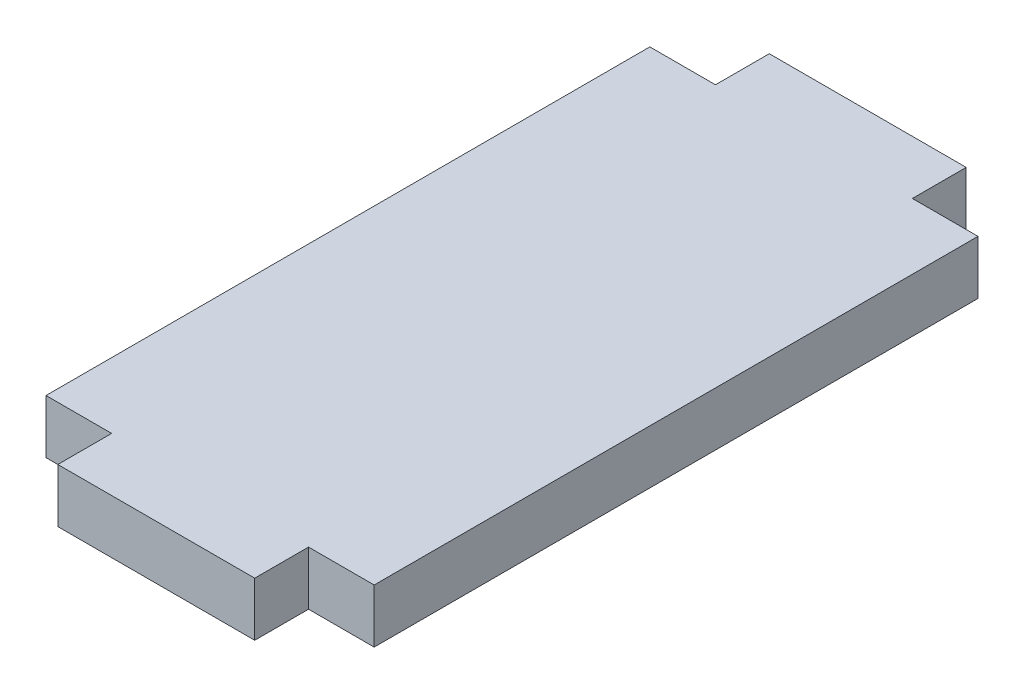
SolidWorks part; units mm, degrees
material "Corrugated Paper"
ref_plane "Front" through (0, 0, 0) normal (0, 0, 1) x (1, 0, 0)
ref_plane "Top" through (0, 0, 0) normal (0, 1, 0) x (1, 0, 0)
ref_plane "Right" through (0, 0, 0) normal (1, 0, 0) x (0, 0, -1)
sketch "Sketch1" plane through (0, 0, 0) normal (0, 1, 0) x (1, 0, 0)
  line L0 (-12.5, 0) -> (12.5, 0) construction
  line L1 (-12.5, -23) -> (12.5, -23) construction
  line L2 (-12.5, -23) -> (-12.5, 23)
  line L3 (-12.5, 23) -> (12.5, 23) construction
  line L4 (12.5, -23) -> (12.5, 23)
  line L5 (-12.5, -23) -> (12.5, 23) construction
  line L6 (-12.5, 23) -> (12.5, -23) construction
  line L7 (-12.5, 23) -> (-7.5, 23)
  line L8 (7.5, -23) -> (7.5, -27.1)
  line L9 (-7.5, 23) -> (-7.5, 27.1)
  line L10 (-7.5, 27.1) -> (7.5, 27.1)
  line L11 (7.5, 23) -> (7.5, 27.1)
  line L12 (7.5, 23) -> (12.5, 23)
  line L13 (-7.5, -27.1) -> (7.5, -27.1)
  line L14 (-7.5, -23) -> (-7.5, -27.1)
  line L15 (-12.5, -23) -> (-7.5, -23)
  line L16 (7.5, -23) -> (12.5, -23)
  point P0 (0, 0)
  dimension "D1" = 25
  dimension "D2" = 15
  dimension "D3" = 4.1
  dimension "D4" = 46
extrude "Boss-Extrude1" add sketch "Sketch1" along normal blind 4.1
